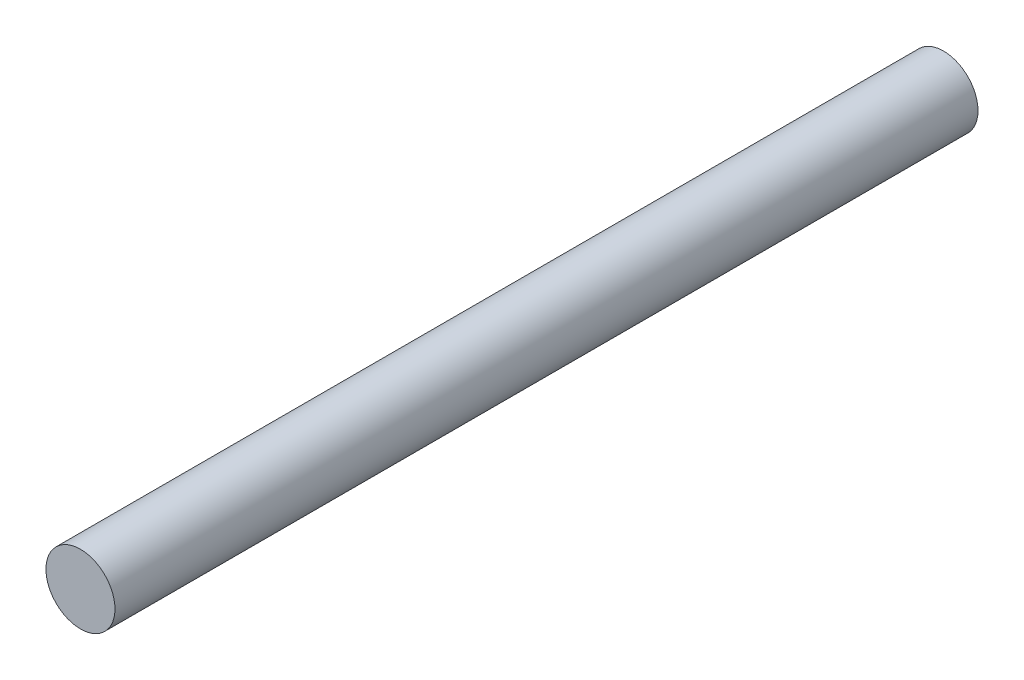
SolidWorks part; units mm, degrees
ref_plane "Front Plane" through (0, 0, 0) normal (0, 0, 1) x (1, 0, 0)
ref_plane "Top Plane" through (0, 0, 0) normal (0, 1, 0) x (1, 0, 0)
ref_plane "Right Plane" through (0, 0, 0) normal (1, 0, 0) x (0, 0, -1)
sketch "Sketch1" plane through (0, 0, 0) normal (0, 0, 1) x (1, 0, 0)
  circle A0 centre (0, 0) radius 1.27
  dimension "D1" = 2.54
extrude "Boss-Extrude1" add sketch "Sketch1" along normal mid plane 31.75
